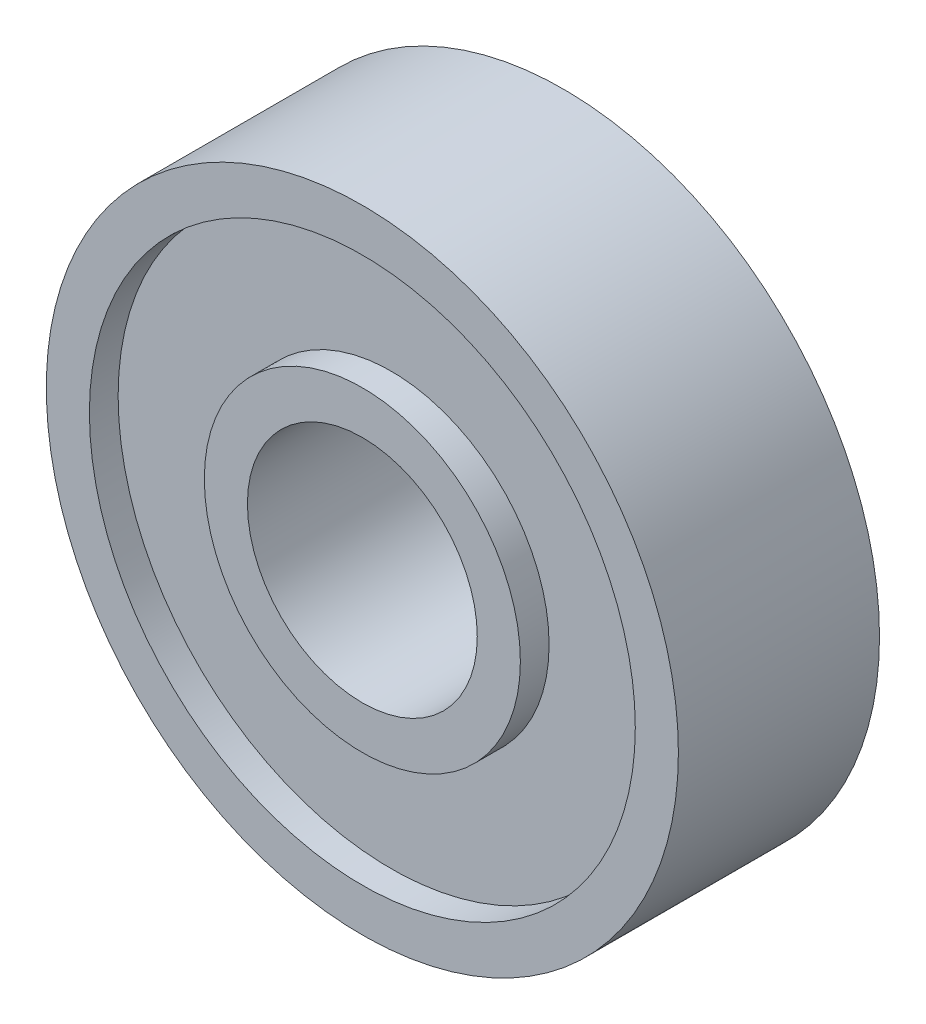
SolidWorks part; units mm, degrees
ref_plane "Front Plane" through (0, 0, 0) normal (0, 0, 1) x (1, 0, 0)
ref_plane "Top Plane" through (0, 0, 0) normal (0, 1, 0) x (1, 0, 0)
ref_plane "Right Plane" through (0, 0, 0) normal (1, 0, 0) x (0, 0, -1)
sketch "Sketch1" plane through (0, 0, 0) normal (0, 0, 1) x (1, 0, 0)
  circle A0 centre (0, 0) radius 4
  circle A1 centre (0, 0) radius 11
  dimension "D1" = 8
  dimension "D2" = 22
extrude "Boss-Extrude1" add sketch "Sketch1" along normal blind 7
sketch "Sketch2" plane through (0, 0, 7) normal (0, 0, 1) x (1, 0, 0)
  circle A0 centre (0, 0) radius 5.5
  circle A1 centre (0, 0) radius 9.5
  circle A2 centre (0, 0) radius 11 construction
  circle A3 centre (0, 0) radius 4 construction
  dimension "D1" = 1.5
  dimension "D2" = 1.5
extrude "Cut-Extrude1" cut sketch "Sketch2" against normal blind 1
sketch "Sketch3" plane through (0, 0, 0) normal (0, 0, -1) x (-1, 0, 0)
  circle A0 centre (0, 0) radius 5.5
  circle A1 centre (0, 0) radius 9.5
extrude "Cut-Extrude2" cut sketch "Sketch3" against normal blind 1
